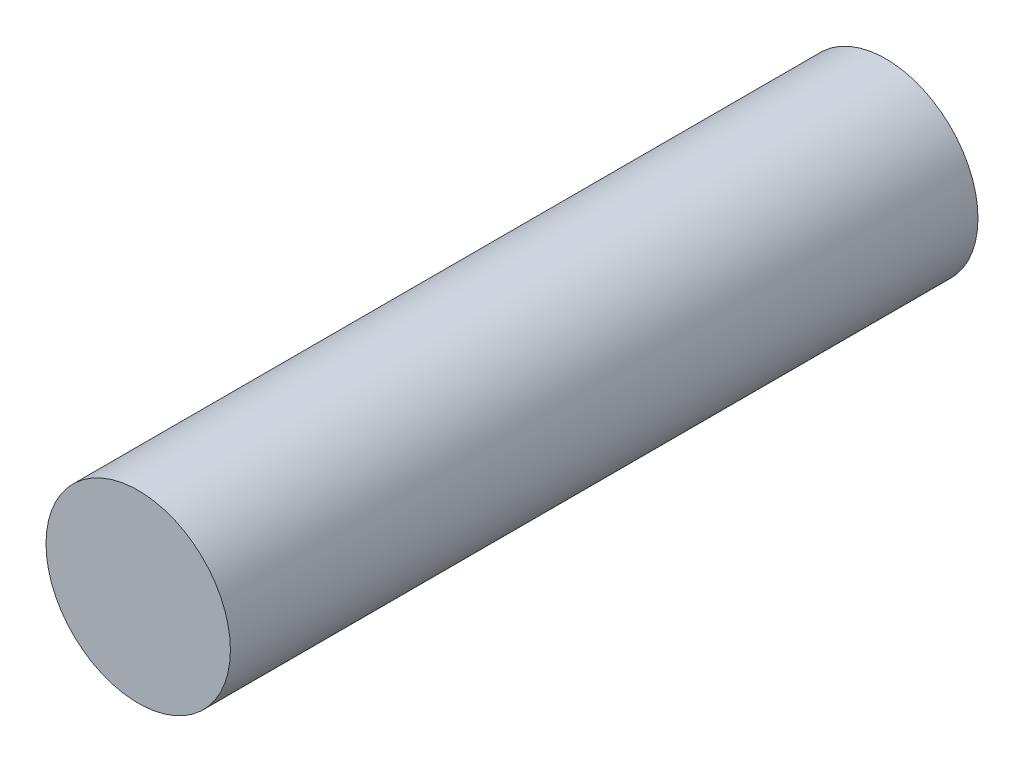
SolidWorks part; units mm, degrees
ref_plane "Front" through (0, 0, 0) normal (0, 0, 1) x (1, 0, 0)
ref_plane "Top" through (0, 0, 0) normal (0, 1, 0) x (1, 0, 0)
ref_plane "Right" through (0, 0, 0) normal (1, 0, 0) x (0, 0, -1)
sketch "Sketch1" plane through (0, 0, 0) normal (0, 0, 1) x (1, 0, 0)
  circle A0 centre (0, 0) radius 4.699
  dimension "D1" = 9.398
extrude "Base-Extrude" add sketch "Sketch1" along normal blind 38.1
